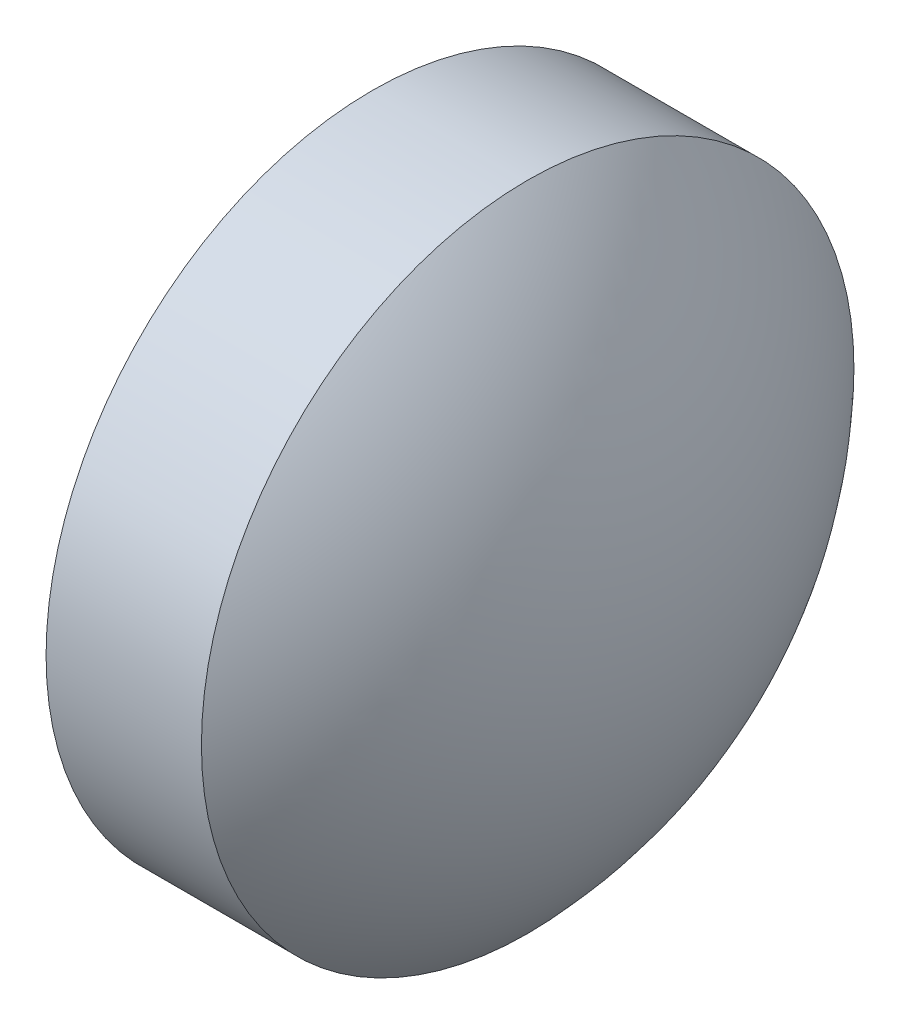
SolidWorks part; units mm, degrees
ref_plane "前视基准面" through (0, 0, 0) normal (0, 0, 1) x (1, 0, 0)
ref_plane "上视基准面" through (0, 0, 0) normal (0, 1, 0) x (1, 0, 0)
ref_plane "右视基准面" through (0, 0, 0) normal (1, 0, 0) x (0, 0, -1)
sketch "草图1" plane through (0, 0, 0) normal (0, 0, 1) x (1, 0, 0)
  line L0 (390.0979, 105.8765) -> (395.4929, 105.8765) construction
  line L1 (390.9585, 105.8765) -> (390.9585, 109.0265)
  line L2 (390.9585, 109.0265) -> (392.4585, 109.0265)
  line L3 (393.7085, 105.8765) -> (390.9585, 105.8765)
  arc A0 (393.7085, 105.8765) -> (392.4585, 109.0265) centre (389.1145, 105.8765) ccw
revolve "旋转1" add sketch "草图1" angle 360 about L0
